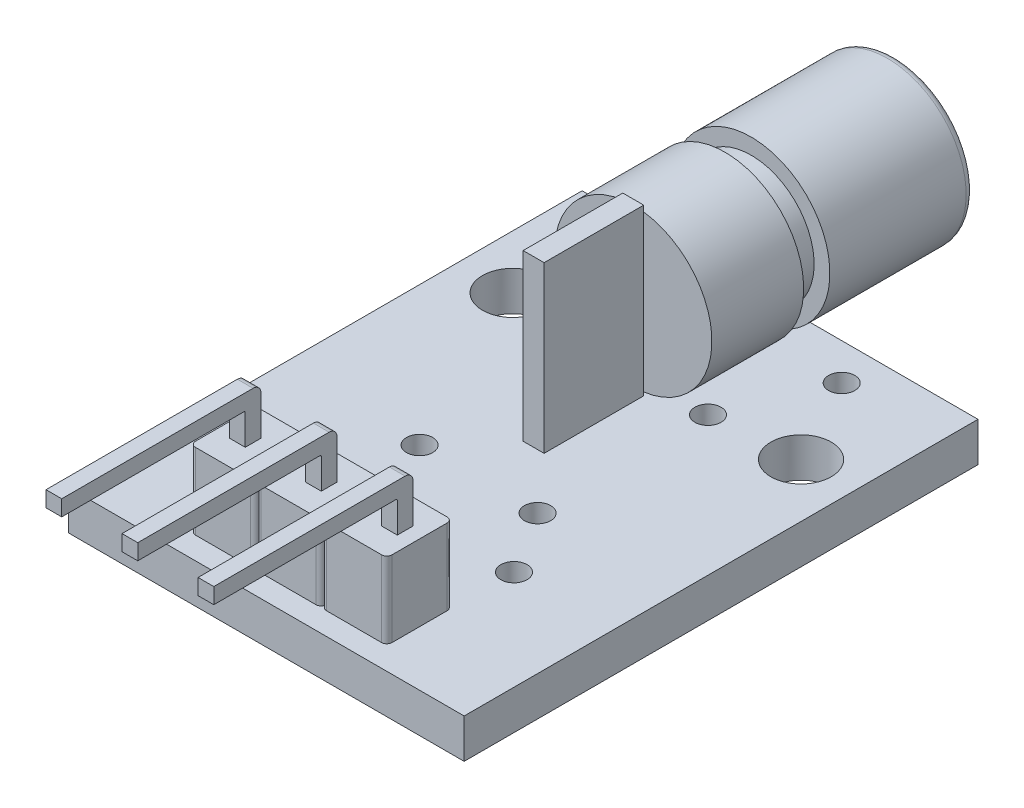
SolidWorks part; units mm, degrees
ref_plane "Front Plane" through (0, 0, 0) normal (0, 0, 1) x (1, 0, 0)
ref_plane "Top Plane" through (0, 0, 0) normal (0, 1, 0) x (1, 0, 0)
ref_plane "Right Plane" through (0, 0, 0) normal (1, 0, 0) x (0, 0, -1)
sketch "Sketch1" plane through (0, 0, 0) normal (0, 1, 0) x (1, 0, 0)
  line L1 (-7.55, -9.8) -> (7.55, -9.8)
  line L2 (-7.55, -9.8) -> (-7.55, 9.8)
  line L3 (-7.55, 9.8) -> (7.55, 9.8)
  line L4 (7.55, -9.8) -> (7.55, 9.8)
  line L5 (-7.55, -9.8) -> (7.55, 9.8) construction
  line L6 (-7.55, 9.8) -> (7.55, -9.8) construction
  point P0 (0, 0)
  dimension "D1" = 15.1
  dimension "D2" = 19.6
extrude "Boss-Extrude1" add sketch "Sketch1" along normal blind 1.5
sketch "Sketch2" plane through (0, 0, 0) normal (0, -1, 0) x (1, 0, 0)
  line L0 (0.3, 7.4) -> (3.2, 7.4) construction
  line L1 (-0.3, 8) -> (0.3, 8)
  line L2 (-0.3, 8) -> (-0.3, 7.4)
  line L3 (-0.3, 7.4) -> (0.3, 7.4)
  line L4 (0.3, 8) -> (0.3, 7.4)
  line L5 (-0.3, 8) -> (0.3, 7.4) construction
  line L6 (-0.3, 7.4) -> (0.3, 8) construction
  line L7 (3.2, 8) -> (2.6, 8)
  line L8 (3.2, 8) -> (3.2, 7.4)
  line L9 (3.2, 7.4) -> (2.6, 7.4)
  line L10 (2.6, 8) -> (2.6, 7.4)
  line L11 (3.2, 8) -> (2.6, 7.4) construction
  line L12 (3.2, 7.4) -> (2.6, 8) construction
  line L13 (-3.2, 8) -> (-2.6, 8)
  line L14 (-3.2, 8) -> (-3.2, 7.4)
  line L15 (-3.2, 7.4) -> (-2.6, 7.4)
  line L16 (-2.6, 8) -> (-2.6, 7.4)
  line L17 (-3.2, 8) -> (-2.6, 7.4) construction
  line L18 (-3.2, 7.4) -> (-2.6, 8) construction
  line L19 (-2.6, 7.4) -> (-0.3, 7.4) construction
  line L20 (0, 0) -> (0, 7.4) construction
  line L21 (-7.55, 9.8) -> (7.55, 9.8) construction
  line L22 (0.3, 8) -> (2.6, 8) construction
  line L23 (-2.6, 8) -> (-0.3, 8) construction
  point P0 (0, 7.7)
  point P5 (2.9, 7.7)
  point P10 (-2.9, 7.7)
  dimension "D1" = 0.6
  dimension "D2" = 0.6
  dimension "D3" = 2.4
  dimension "D4" = 5.8
extrude "Boss-Extrude2" add sketch "Sketch2" along normal blind 1.7
sketch "Sketch3" plane through (0, 1.5, 0) normal (0, 1, 0) x (1, 0, 0)
  line L0 (0.3, -8) -> (-0.3, -7.4) construction
  line L2 (-3.75, -8.95) -> (-3.75, -6.45)
  line L4 (3.75, -8.95) -> (3.75, -6.45)
  line L5 (-3.75, -8.95) -> (3.75, -6.45) construction
  line L6 (-3.75, -6.45) -> (3.75, -8.95) construction
  line L7 (-3.75, -6.45) -> (-1.45, -6.45)
  line L8 (-1.05, -6.45) -> (1.05, -6.45)
  line L9 (1.45, -6.45) -> (3.75, -6.45)
  line L10 (-1.05, -6.45) -> (-1.45, -6.45) construction
  line L11 (1.45, -6.45) -> (1.05, -6.45) construction
  line L12 (-3.75, -8.95) -> (-1.45, -8.95)
  line L13 (-1.05, -8.95) -> (1.05, -8.95)
  line L14 (1.45, -8.95) -> (3.75, -8.95)
  line L15 (-1.05, -8.95) -> (-1.45, -8.95) construction
  line L16 (1.45, -8.95) -> (1.05, -8.95) construction
  line L17 (-1.25, -8.75) -> (-1.25, -6.65) construction
  line L18 (1.25, -8.75) -> (1.25, -6.65) construction
  line L19 (1.25, -8.75) -> (-1.25, -8.75) construction
  line L20 (1.25, -6.65) -> (-1.25, -6.65) construction
  line L21 (0, -7.7) -> (0, -8.95) construction
  arc A0 (-1.45, -6.45) -> (-1.25, -6.65) centre (-1.45, -6.65) cw
  arc A1 (-1.25, -6.65) -> (-1.05, -6.45) centre (-1.05, -6.65) cw
  arc A2 (1.05, -6.45) -> (1.25, -6.65) centre (1.05, -6.65) cw
  arc A3 (1.25, -6.65) -> (1.45, -6.45) centre (1.45, -6.65) cw
  arc A4 (-1.45, -8.95) -> (-1.25, -8.75) centre (-1.45, -8.75) ccw
  arc A5 (-1.25, -8.75) -> (-1.05, -8.95) centre (-1.05, -8.75) ccw
  arc A6 (1.05, -8.95) -> (1.25, -8.75) centre (1.05, -8.75) ccw
  arc A7 (1.25, -8.75) -> (1.45, -8.95) centre (1.45, -8.75) ccw
  point P0 (0, -7.7)
  dimension "D3" = 0.2
  dimension "D4" = 0.2
  dimension "D1" = 7.5
  dimension "D2" = 2.5
extrude "Boss-Extrude3" add sketch "Sketch3" along normal blind 2.9
sketch "Sketch4" plane through (0, 4.4, 0) normal (0, 1, 0) x (1, 0, 0)
  line L1 (-3.2, -8) -> (-2.6, -8)
  line L2 (-3.2, -8) -> (-3.2, -7.4)
  line L3 (-3.2, -7.4) -> (-2.6, -7.4)
  line L4 (-2.6, -8) -> (-2.6, -7.4)
  line L5 (-0.3, -8) -> (0.3, -8)
  line L6 (-0.3, -8) -> (-0.3, -7.4)
  line L7 (-0.3, -7.4) -> (0.3, -7.4)
  line L8 (0.3, -8) -> (0.3, -7.4)
  line L9 (2.6, -8) -> (3.2, -8)
  line L10 (2.6, -8) -> (2.6, -7.4)
  line L11 (2.6, -7.4) -> (3.2, -7.4)
  line L12 (3.2, -8) -> (3.2, -7.4)
extrude "Boss-Extrude4" add sketch "Sketch4" along normal blind 1.8
sketch "Sketch5" plane through (0, 0, 8) normal (0, 0, 1) x (1, 0, 0)
  line L0 (-2.6, 6.2) -> (-2.6, 4.4) construction
  line L1 (-3.2, 6.2) -> (-2.6, 6.2)
  line L2 (-3.2, 6.2) -> (-3.2, 5.6)
  line L3 (-3.2, 5.6) -> (-2.6, 5.6)
  line L4 (-2.6, 6.2) -> (-2.6, 5.6)
  line L5 (0.3, 6.2) -> (0.3, 4.4) construction
  line L6 (-0.3, 6.2) -> (0.3, 6.2)
  line L7 (-0.3, 6.2) -> (-0.3, 5.6)
  line L8 (-0.3, 5.6) -> (0.3, 5.6)
  line L9 (0.3, 6.2) -> (0.3, 5.6)
  line L10 (3.2, 6.2) -> (3.2, 4.4) construction
  line L11 (2.6, 6.2) -> (3.2, 6.2)
  line L12 (2.6, 6.2) -> (2.6, 5.6)
  line L13 (2.6, 5.6) -> (3.2, 5.6)
  line L14 (3.2, 6.2) -> (3.2, 5.6)
  line L15 (-2.6, 5.6) -> (-0.3, 5.6) construction
  line L16 (0.3, 5.6) -> (2.6, 5.6) construction
extrude "Boss-Extrude5" add sketch "Sketch5" along normal blind 7
sketch "Sketch7" plane through (0, 1.5, 0) normal (0, 1, 0) x (1, 0, 0)
  line L0 (7.55, 9.8) -> (-7.55, 9.8) construction
  line L1 (0.4, 4.2) -> (-0.4, 4.2)
  line L2 (0.4, 4.2) -> (0.4, 0.4)
  line L3 (0.4, 0.4) -> (-0.4, 0.4)
  line L4 (-0.4, 4.2) -> (-0.4, 0.4)
  line L5 (0.4, 4.2) -> (-0.4, 0.4) construction
  line L6 (0.4, 0.4) -> (-0.4, 4.2) construction
  line L7 (0, 0) -> (0, 0.4) construction
  point P0 (0, 2.3)
  dimension "D1" = 9.4
  dimension "D2" = 3.8
  dimension "D3" = 0.8
extrude "Boss-Extrude6" add sketch "Sketch7" along normal blind 6.3
sketch "Sketch8" plane through (0, 0, -4.2) normal (0, 0, -1) x (-1, 0, 0)
  line L0 (0, 4.6) -> (0, 0) construction
  circle A0 centre (0, 4.6) radius 3
  dimension "D1" = 6
  dimension "D2" = 4.6
extrude "Boss-Extrude7" add sketch "Sketch8" along normal blind 3.5
sketch "Sketch9" plane through (0, 0, -7.7) normal (0, 0, -1) x (-1, 0, 0)
  circle A0 centre (0, 4.6) radius 2.4
  dimension "D1" = 4.8
extrude "Boss-Extrude8" add sketch "Sketch9" along normal blind 1
sketch "Sketch10" plane through (0, 0, -8.7) normal (0, 0, -1) x (-1, 0, 0)
  circle A0 centre (0, 4.6) radius 3
  circle A1 centre (0, 4.6) radius 3 construction
extrude "Boss-Extrude9" add sketch "Sketch10" along normal blind 5.5
fillet "Fillet1" radius 0.3 1 edges at (-3, 4.6, -14.2)
sketch "Sketch11" plane through (0, 0, -14.2) normal (0, 0, -1) x (-1, 0, 0)
  circle A0 centre (0, 4.6) radius 1.5
  dimension "D1" = 3
extrude "Cut-Extrude1" cut sketch "Sketch11" against normal blind 1
sketch "Sketch12" plane through (0, 1.5, 0) normal (0, 1, 0) x (1, 0, 0)
  line L0 (-5.5, 5.1) -> (5.5, 5.1) construction
  line L1 (7.55, 9.8) -> (-7.55, 9.8) construction
  line L2 (0, 5.1) -> (0, 0) construction
  circle A0 centre (-5.5, 5.1) radius 1.15
  circle A1 centre (5.5, 5.1) radius 1.15
  dimension "D2" = 2.3
  dimension "D1" = 4.7
  dimension "D3" = 11
extrude "Cut-Extrude2" cut sketch "Sketch12" against normal through all
sketch "Sketch13" plane through (0, 0, 0) normal (0, -1, 0) x (1, 0, 0)
  line L0 (2.25, 1.7) -> (-2.25, -4.8) construction
  line L1 (2.25, 1.7) -> (-2.25, 1.7) construction
  line L2 (2.25, 1.7) -> (2.25, -4.8) construction
  line L3 (2.25, -4.8) -> (-2.25, -4.8) construction
  line L4 (-2.25, 1.7) -> (-2.25, -4.8) construction
  line L5 (-2.25, 1.7) -> (2.25, -4.8) construction
  line L6 (7.55, -9.8) -> (-7.55, -9.8) construction
  line L7 (0, 0) -> (0, -4.8) construction
  circle A0 centre (-2.25, -4.8) radius 0.5
  circle A1 centre (2.25, -4.8) radius 0.5
  circle A2 centre (2.25, 1.7) radius 0.5
  circle A3 centre (-2.25, 1.7) radius 0.5
  dimension "D3" = 1
  dimension "D1" = 5
  dimension "D2" = 6.5
  dimension "D4" = 4.5
extrude "Cut-Extrude3" cut sketch "Sketch13" against normal up to next
sketch "Sketch14" plane through (0, 0, 0) normal (0, -1, 0) x (1, 0, 0)
  line L0 (0, 0) -> (0, -2.15) construction
  line L1 (-3.75, -8.4) -> (3.75, -8.4) construction
  line L2 (-3.75, -8.4) -> (-3.75, 4.1) construction
  line L3 (-3.75, 4.1) -> (3.75, 4.1) construction
  line L4 (3.75, -8.4) -> (3.75, 4.1) construction
  line L5 (-3.75, -8.4) -> (3.75, 4.1) construction
  line L6 (-3.75, 4.1) -> (3.75, -8.4) construction
  line L7 (7.55, -9.8) -> (-7.55, -9.8) construction
  circle A0 centre (3.75, 4.1) radius 0.5
  circle A1 centre (-3.75, 4.1) radius 0.5
  circle A2 centre (-3.75, -8.4) radius 0.5
  circle A3 centre (3.75, -8.4) radius 0.5
  point P0 (0, -2.15)
  dimension "D1" = 1
  dimension "D2" = 7.5
  dimension "D3" = 12.5
  dimension "D4" = 1.4
extrude "Cut-Extrude4" cut sketch "Sketch14" against normal up to next
fillet "Fillet2" radius 0.2 4 edges at (3.75, 2.95, 6.45) (3.75, 2.95, 8.95) (-3.75, 2.95, 8.95) (-3.75, 2.95, 6.45)
fillet "Fillet3" radius 0.05 3 edges at (-2.9, 5.6, 8) (0, 5.6, 8) (2.9, 5.6, 8)
fillet "Fillet5" radius 0.3 3 edges at (2.9, 6.2, 7.4) (-2.9, 6.2, 7.4) (0, 6.2, 7.4)
